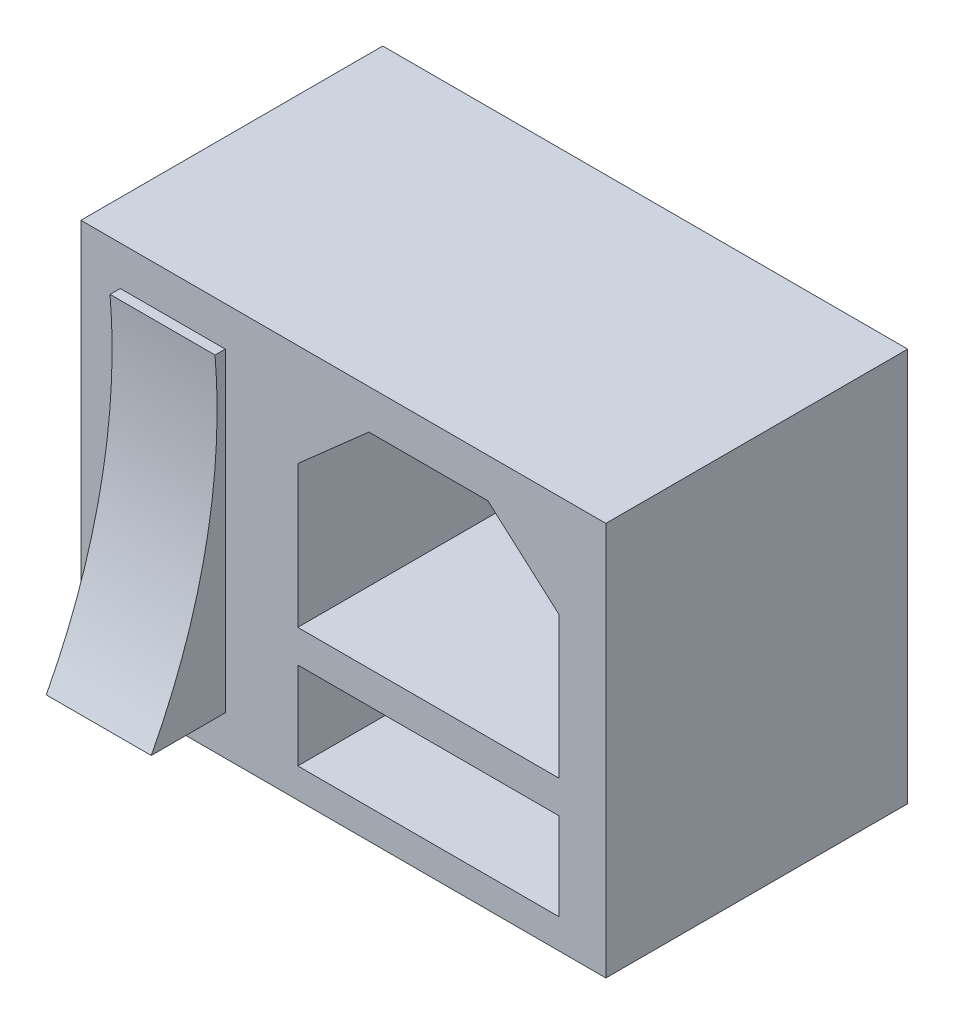
SolidWorks part; units mm, degrees
ref_plane "Ön Düzlem" through (0, 0, 0) normal (0, 0, 1) x (1, 0, 0)
ref_plane "Üst Düzlem" through (0, 0, 0) normal (0, 1, 0) x (1, 0, 0)
ref_plane "Sağ Düzlem" through (0, 0, 0) normal (1, 0, 0) x (0, 0, -1)
sketch "Sketch1" plane through (0, 0, 0) normal (0, 0, 1) x (1, 0, 0)
  line L1 (-20, 15) -> (20, 15)
  line L2 (-20, 15) -> (-20, -15)
  line L3 (-20, -15) -> (20, -15)
  line L4 (20, 15) -> (20, -15)
  line L5 (-20, 15) -> (20, -15) construction
  line L6 (-20, -15) -> (20, 15) construction
  point P0 (0, 0)
  dimension "D1" = 40
  dimension "D2" = 30
extrude "Boss-Extrude1" add sketch "Sketch1" along normal blind 23
sketch "Sketch2" plane through (0, 0, 23) normal (0, 0, 1) x (1, 0, 0)
  line L0 (-3.4753, 7.2085) -> (-3.4753, -3.5995)
  line L1 (-3.4753, -3.5995) -> (16.4251, -3.5995)
  line L2 (16.4251, -3.5995) -> (16.4251, 7.2085)
  line L3 (16.4251, 7.2085) -> (11.0052, 11.9982)
  line L4 (11.0052, 11.9982) -> (1.9445, 11.9982)
  line L5 (1.9445, 11.9982) -> (-3.4753, 7.2085)
  line L6 (-3.4753, -6.0818) -> (-3.4753, -12.7429)
  line L7 (-3.4753, -12.7429) -> (16.4251, -12.7429)
  line L8 (16.4251, -12.7429) -> (16.4251, -6.0818)
  line L9 (16.4251, -6.0818) -> (-3.4753, -6.0818)
  point P8 (6.4749, 11.9982)
  point P11 (6.4749, -3.5995)
extrude "Cut-Extrude1" cut sketch "Sketch2" against normal blind 19
sketch "Sketch3" plane through (0, -12.7429, 0) normal (0, 1, 0) x (1, 0, 0)
  line L0 (20, -23) -> (-20, -23) construction
  circle A0 centre (6.5783, -13) radius 2
  dimension "D1" = 4
  dimension "D2" = 10
extrude "Cut-Extrude2" cut sketch "Sketch3" against normal blind 19
ref_plane "Plane1" through (-17, 0, 0) normal (-1, 0, 0) x (0, 0, 1)
sketch "Sketch4" plane through (-17, 0, 0) normal (-1, 0, 0) x (0, 0, 1)
  line L0 (23, 12) -> (23.7782, 12)
  line L1 (23, 15) -> (23, -15) construction
  line L2 (23, -12) -> (28.6371, -12)
  line L3 (23, 12) -> (23, -12)
  line L4 (23, 15) -> (0, 15) construction
  line L5 (23, -15) -> (0, -15) construction
  arc A0 (28.6371, -12) -> (23.7782, 12) centre (67.179, 8.2948) cw
  dimension "D1" = 3
  dimension "D2" = 3
extrude "Boss-Extrude2" add sketch "Sketch4" against normal blind 8
